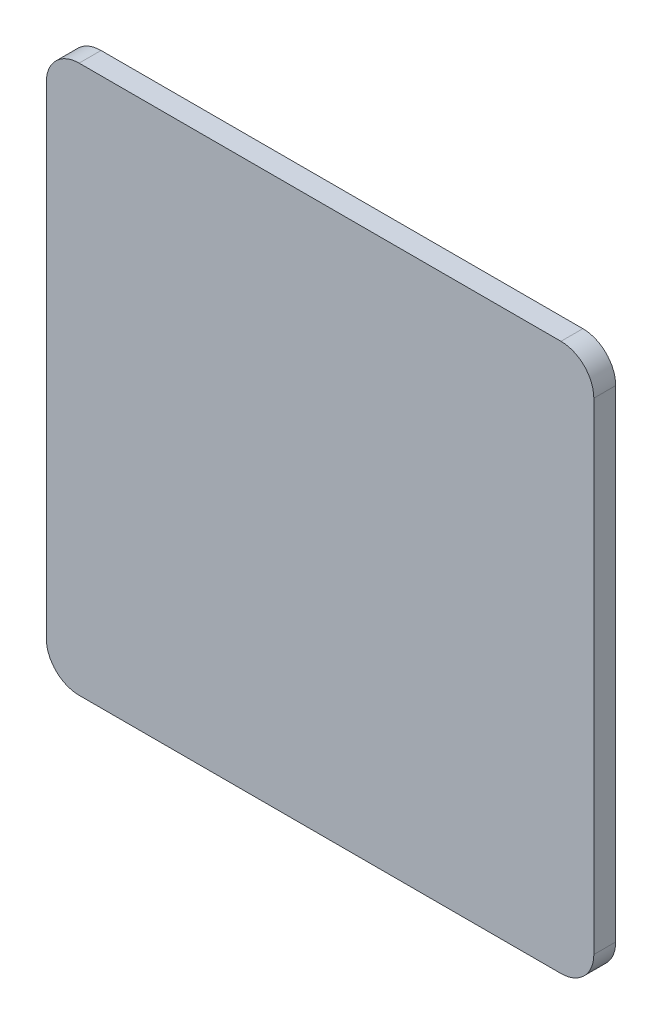
SolidWorks part; units mm, degrees
material "Beech"
ref_plane "Front Plane" through (0, 0, 0) normal (0, 0, 1) x (1, 0, 0)
ref_plane "Top Plane" through (0, 0, 0) normal (0, 1, 0) x (1, 0, 0)
ref_plane "Right Plane" through (0, 0, 0) normal (1, 0, 0) x (0, 0, -1)
sketch "Sketch1" plane through (0, 0, 0) normal (0, 0, 1) x (1, 0, 0)
  line L1 (63.5, 63.5) -> (-63.5, 63.5)
  line L2 (63.5, 63.5) -> (63.5, -63.5)
  line L3 (63.5, -63.5) -> (-63.5, -63.5)
  line L4 (-63.5, 63.5) -> (-63.5, -63.5)
  line L5 (63.5, 63.5) -> (-63.5, -63.5) construction
  line L6 (63.5, -63.5) -> (-63.5, 63.5) construction
  point P0 (0, 0)
  dimension "D1" = 127
  dimension "D2" = 127
extrude "Boss-Extrude1" add sketch "Sketch1" along normal blind 5.08
fillet "Fillet1" radius 7.62 4 edges at (-63.5, -63.5, 2.54) (63.5, -63.5, 2.54) (63.5, 63.5, 2.54) (-63.5, 63.5, 2.54)
